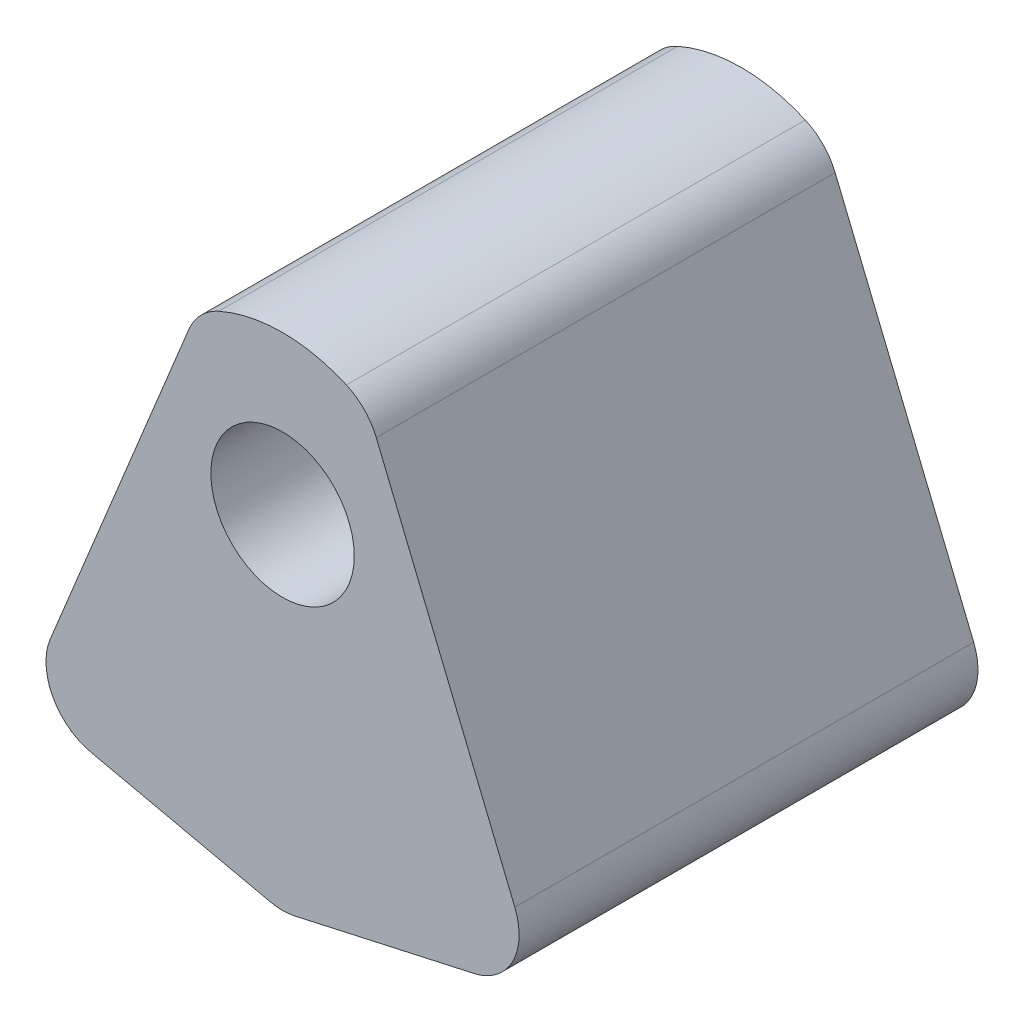
SolidWorks part; units mm, degrees
ref_plane "Front Plane" through (0, 0, 0) normal (0, 0, 1) x (1, 0, 0)
ref_plane "Top Plane" through (0, 0, 0) normal (0, 1, 0) x (1, 0, 0)
ref_plane "Right Plane" through (0, 0, 0) normal (1, 0, 0) x (0, 0, -1)
sketch "Szkic1" plane through (0, 0, 0) normal (0, 0, 1) x (1, 0, 0)
  line L0 (0, 0) -> (0, 8.3049) construction
  line L1 (0.2169, 0.0482) -> (3.3408, 0.7424)
  line L2 (4.0489, 2.0985) -> (1.6334, 7.9801)
  line L3 (-4.0489, 2.0985) -> (-1.6334, 7.9801)
  line L4 (-0.2169, 0.0482) -> (-3.3408, 0.7424)
  circle A0 centre (0, 6) radius 1.25
  arc A2 (1.1131, 8.5147) -> (-1.1131, 8.5147) centre (0, 6) ccw
  arc A3 (4.0489, 2.0985) -> (3.3408, 0.7424) centre (3.1238, 1.7186) cw
  arc A4 (-3.3408, 0.7424) -> (-4.0489, 2.0985) centre (-3.1238, 1.7186) cw
  arc A5 (1.1131, 8.5147) -> (1.6334, 7.9801) centre (0.7083, 7.6002) cw
  arc A6 (-1.1131, 8.5147) -> (-1.6334, 7.9801) centre (-0.7083, 7.6002) ccw
  arc A7 (0.2169, 0.0482) -> (-0.2169, 0.0482) centre (0, 1.0244) cw
  point P14 (4.5, 1)
  point P17 (-4.5, 1)
  point P20 (1.5, 8.3049)
  point P23 (-1.5, 8.3049)
  dimension "D2" = 2.5
  dimension "D3" = 1
  dimension "D7" = 1
  dimension "D8" = 2.75
  dimension "D1" = 6
  dimension "D4" = 1
  dimension "D5" = 4.5
  dimension "D6" = 1.5
extrude "Dodanie-wyciągnięcie1" add sketch "Szkic1" along normal blind 8
